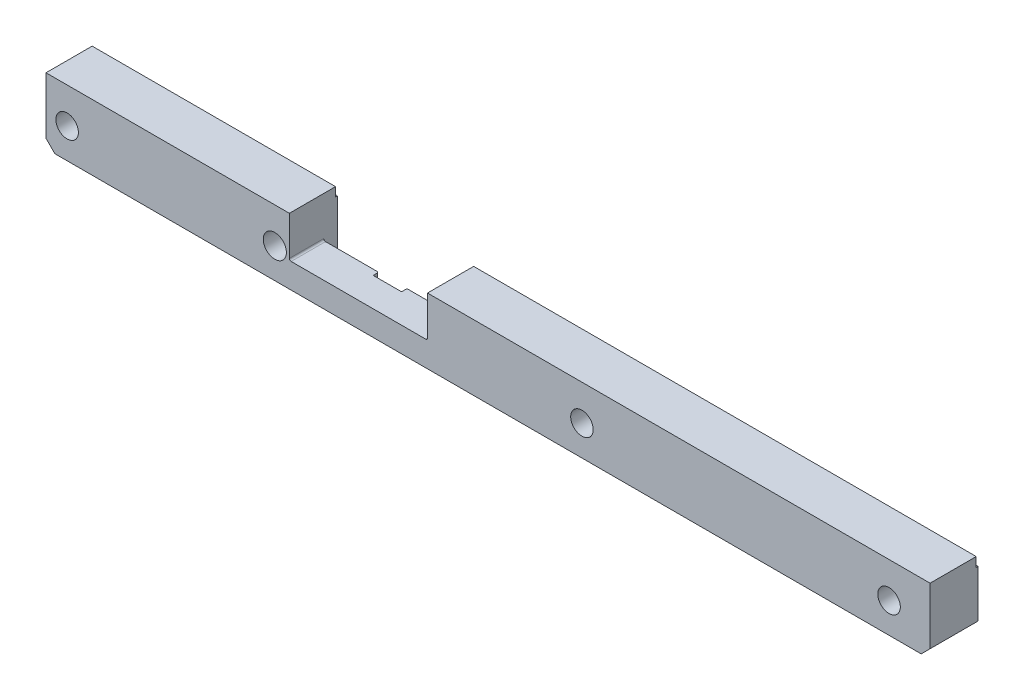
SolidWorks part; units mm, degrees
ref_plane "Front Plane" through (0, 0, 0) normal (0, 0, 1) x (1, 0, 0)
ref_plane "Top Plane" through (0, 0, 0) normal (0, 1, 0) x (1, 0, 0)
ref_plane "Right Plane" through (0, 0, 0) normal (1, 0, 0) x (0, 0, -1)
sketch "Sketch1" plane through (0, 0, 0) normal (0, 0, 1) x (1, 0, 0)
  line L1 (-151.0977, 41.5943) -> (346.9023, 41.5943)
  line L2 (-151.0977, 41.5943) -> (-151.0977, 4.5943)
  line L3 (-151.0977, 4.5943) -> (346.9023, 4.5943)
  line L4 (346.9023, 41.5943) -> (346.9023, 4.5943)
  dimension "D1" = 498
  dimension "D2" = 37
extrude "Boss-Extrude1" add sketch "Sketch1" along normal blind 27
sketch "Sketch3" plane through (0, 0, 0) normal (0, 0, -1) x (-1, 0, 0)
  line L0 (151.0977, 4.5943) -> (-346.9023, 4.5943) construction
  line L1 (-264.9023, 4.5943) -> (-294.9023, 4.5943)
  line L2 (-264.9023, 4.5943) -> (-264.9023, 31.5943)
  line L3 (-264.9023, 31.5943) -> (-294.9023, 31.5943)
  line L4 (-294.9023, 4.5943) -> (-294.9023, 31.5943)
  line L5 (-346.9023, 4.5943) -> (-346.9023, 41.5943) construction
  dimension "D1" = 27
  dimension "D2" = 52
  dimension "D3" = 82
extrude "Cut-Extrude2" cut sketch "Sketch3" against normal blind 4
sketch "Sketch4" plane through (0, 0, 0) normal (0, 0, -1) x (-1, 0, 0)
  line L0 (-346.9023, 41.5943) -> (151.0977, 41.5943) construction
  line L1 (13.9977, 41.5943) -> (-63.8023, 41.5943)
  line L2 (13.9977, 41.5943) -> (13.9977, 18.5943)
  line L3 (13.9977, 18.5943) -> (-63.8023, 18.5943)
  line L4 (-63.8023, 41.5943) -> (-63.8023, 18.5943)
  line L5 (-346.9023, 4.5943) -> (-346.9023, 41.5943) construction
  dimension "D1" = 283.1
  dimension "D2" = 360.9
  dimension "D3" = 23
extrude "Cut-Extrude3" cut sketch "Sketch4" against normal through all
sketch "Sketch5" plane through (0, 18.5943, 0) normal (0, 1, 0) x (1, 0, 0)
  line L0 (63.8023, -27) -> (63.8023, 0) construction
  line L1 (-13.9977, 0) -> (63.8023, 0)
  line L2 (-13.9977, 0) -> (-13.9977, -7.65)
  line L3 (-13.9977, -7.65) -> (63.8023, -7.65)
  line L4 (63.8023, 0) -> (63.8023, -7.65)
  line L5 (63.8023, -27) -> (-13.9977, -27) construction
  dimension "D1" = 19.35
extrude "Cut-Extrude4" cut sketch "Sketch5" against normal through all
sketch "Sketch6" plane through (0, 0, 7.65) normal (0, 0, -1) x (-1, 0, 0)
  line L0 (13.9977, 4.5943) -> (-63.8023, 4.5943) construction
  line L1 (-16.9023, 4.5943) -> (-32.9023, 4.5943)
  line L2 (-16.9023, 4.5943) -> (-16.9023, 18.5943)
  line L3 (-16.9023, 18.5943) -> (-32.9023, 18.5943)
  line L4 (-32.9023, 4.5943) -> (-32.9023, 18.5943)
  line L5 (13.9977, 18.5943) -> (-63.8023, 18.5943) construction
  line L6 (-346.9023, 4.5943) -> (-346.9023, 41.5943) construction
  point P10 (-16.9023, 11.5943)
  dimension "D1" = 314
  dimension "D2" = 330
extrude "Cut-Extrude5" cut sketch "Sketch6" against normal blind 3.05
sketch "Sketch7" plane through (0, 0, 0) normal (0, 0, -1) x (-1, 0, 0)
  line L0 (151.0977, 36.2546) -> (146.0977, 37.5943)
  line L1 (151.0977, 41.5943) -> (151.0977, 4.5943) construction
  line L2 (146.0977, 37.5943) -> (18.2423, 37.5943)
  line L3 (18.2423, 37.5943) -> (13.9977, 36.457)
  line L4 (13.9977, 4.5943) -> (13.9977, 41.5943) construction
  line L5 (13.9977, 36.457) -> (13.9977, 37.5943)
  line L6 (13.9977, 37.5943) -> (-63.8023, 37.5943)
  line L7 (-63.8023, 41.5943) -> (-63.8023, 4.5943) construction
  line L8 (-63.8023, 37.5943) -> (-341.9023, 37.5943)
  line L11 (-341.9023, 37.5943) -> (-346.9023, 36.2546)
  line L12 (-346.9023, 4.5943) -> (-346.9023, 41.5943) construction
  line L13 (-346.9023, 36.2546) -> (-346.9023, 41.5943)
  line L14 (-346.9023, 41.5943) -> (151.0977, 41.5943)
  line L15 (151.0977, 41.5943) -> (151.0977, 36.2546)
  dimension "D1" = 5
  dimension "D2" = 15
  dimension "D3" = 15
  dimension "D4" = 4
  dimension "D5" = 4
  dimension "D6" = 5
extrude "Cut-Extrude6" cut sketch "Sketch7" against normal blind 1
hole_wizard "M3 Tapped Hole1" positions "Sketch8" profile "Sketch9" tap size "M3" standard "ISO"
sketch "Sketch8" plane through (0, 4.5943, 0) normal (0, -1, 0) x (-1, 0, 0)
  line L0 (-346.9023, -27) -> (-346.9023, 0) construction
  line L1 (151.0977, -27) -> (-346.9023, -27) construction
  point P0 (-286.4023, -11.76)
  point P2 (-273.4023, -11.76)
  dimension "D1" = 60.5
  dimension "D2" = 73.5
  dimension "D3" = 15.24
sketch "Sketch9" plane through (286.4023, 4.5943, 11.76) normal (1, 0, 0) x (0, 0, -1)
  line L0 (0, 0) -> (0, 6.7511)
  line L1 (0, 6.7511) -> (1.25, 6)
  line L2 (1.25, 6) -> (1.25, 0)
  line L5 (1.25, 0) -> (0, 0)
  line L10 (0, 6.7511) -> (-1.25, 6) construction
  line L11 (0, -6.35) -> (0, 107.95) construction
  dimension "Tap Drill Dia." = 2.5
  dimension "Tap Drill Depth" = 6
  dimension "Drill Angle" = 118
cosmetic thread "Hole Thread1" parameters "D1"=6, "D2"=3
cosmetic thread "Hole Thread2" parameters "D1"=6, "D2"=3
hole_wizard "M4 Tapped Hole1" positions "Sketch10" profile "Sketch11" tap size "M4" standard "ISO"
sketch "Sketch10" plane through (0, 0, 7.65) normal (0, 0, -1) x (-1, 0, 0)
  line L0 (-346.9023, 4.5943) -> (-346.9023, 36.2546) construction
  line L1 (13.9977, 18.5943) -> (-16.9023, 18.5943) construction
  line L2 (-32.9023, 18.5943) -> (-63.8023, 18.5943) construction
  point P0 (5.0977, 11.5943)
  point P2 (-54.9023, 11.5943)
  dimension "D1" = 352
  dimension "D2" = 292
  dimension "D3" = 7
  dimension "D4" = 7
sketch "Sketch11" plane through (-5.0977, 11.5943, 7.65) normal (1, 0, 0) x (0, 1, 0)
  line L0 (0, 0) -> (0, 8.9914)
  line L1 (0, 8.9914) -> (1.65, 8)
  line L2 (1.65, 8) -> (1.65, 0)
  line L5 (1.65, 0) -> (0, 0)
  line L10 (0, 8.9914) -> (-1.65, 8) construction
  line L11 (0, -6.35) -> (0, 107.95) construction
  dimension "Tap Drill Dia." = 3.3
  dimension "Tap Drill Depth" = 8
  dimension "Drill Angle" = 118
cosmetic thread "Hole Thread3" parameters "D1"=8, "D2"=4
cosmetic thread "Hole Thread4" parameters "D1"=8, "D2"=4
hole_wizard "M3 Tapped Hole2" positions "Sketch12" profile "Sketch13" tap size "M3" standard "ISO"
sketch "Sketch12" plane through (0, 0, 0) normal (0, 0, -1) x (-1, 0, 0)
  line L0 (151.0977, 41.5943) -> (13.9977, 41.5943) construction
  line L1 (-346.9023, 4.5943) -> (-346.9023, 36.2546) construction
  point P0 (71.0977, 31.5943)
  point P2 (41.0977, 31.5943)
  point P4 (-99.9023, 31.5943)
  point P6 (-151.9023, 31.5943)
  point P8 (-206.9023, 31.5943)
  point P10 (-221.9023, 31.5943)
  point P12 (-354.5924, -112.4577)
  dimension "D1" = 10
  dimension "D2" = 418
  dimension "D3" = 388
  dimension "D4" = 247
  dimension "D5" = 195
  dimension "D6" = 140
  dimension "D7" = 125
sketch "Sketch13" plane through (-71.0977, 31.5943, 0) normal (1, 0, 0) x (0, 1, 0)
  line L0 (0, 0) -> (0, 6.7511)
  line L1 (0, 6.7511) -> (1.25, 6)
  line L2 (1.25, 6) -> (1.25, 0)
  line L5 (1.25, 0) -> (0, 0)
  line L10 (0, 6.7511) -> (-1.25, 6) construction
  line L11 (0, -6.35) -> (0, 107.95) construction
  dimension "Tap Drill Dia." = 2.5
  dimension "Tap Drill Depth" = 6
  dimension "Drill Angle" = 118
cosmetic thread "Hole Thread5" parameters "D1"=6, "D2"=3
cosmetic thread "Hole Thread6" parameters "D1"=6, "D2"=3
cosmetic thread "Hole Thread7" parameters "D1"=6, "D2"=3
cosmetic thread "Hole Thread8" parameters "D1"=6, "D2"=3
cosmetic thread "Hole Thread9" parameters "D1"=6, "D2"=3
cosmetic thread "Hole Thread10" parameters "D1"=6, "D2"=3
hole_wizard "M3 Tapped Hole3" positions "Sketch14" profile "Sketch15" tap size "M3" standard "ISO"
sketch "Sketch14" plane through (0, 4.5943, 0) normal (0, -1, 0) x (-1, 0, 0)
  line L0 (-346.9023, -27) -> (-346.9023, 0) construction
  line L1 (151.0977, -27) -> (-346.9023, -27) construction
  point P0 (12.3977, -14.1)
  point P2 (4.3977, -14.1)
  dimension "D1" = 359.3
  dimension "D2" = 351.3
  dimension "D3" = 12.9
  dimension "D4" = 12.9
sketch "Sketch15" plane through (-12.3977, 4.5943, 14.1) normal (1, 0, 0) x (0, 0, -1)
  line L0 (0, 0) -> (0, 6.7511)
  line L1 (0, 6.7511) -> (1.25, 6)
  line L2 (1.25, 6) -> (1.25, 0)
  line L5 (1.25, 0) -> (0, 0)
  line L10 (0, 6.7511) -> (-1.25, 6) construction
  line L11 (0, -6.35) -> (0, 107.95) construction
  dimension "Tap Drill Dia." = 2.5
  dimension "Tap Drill Depth" = 6
  dimension "Drill Angle" = 118
cosmetic thread "Hole Thread11" parameters "D1"=6, "D2"=3
cosmetic thread "Hole Thread12" parameters "D1"=6, "D2"=3
sketch "Sketch16" plane through (0, 0, 0) normal (0, 0, -1) x (-1, 0, 0)
  line L0 (-63.8023, 4.5943) -> (-264.9023, 4.5943) construction
  line L1 (-79.4023, 4.5943) -> (-89.4023, 4.5943)
  line L2 (-79.4023, 4.5943) -> (-79.4023, 37.5943)
  line L3 (-79.4023, 37.5943) -> (-89.4023, 37.5943)
  line L4 (-89.4023, 4.5943) -> (-89.4023, 37.5943)
  line L5 (-341.9023, 37.5943) -> (-63.8023, 37.5943) construction
  line L6 (-346.9023, 4.5943) -> (-346.9023, 36.2546) construction
  dimension "D1" = 267.5
  dimension "D2" = 10
extrude "Cut-Extrude7" cut sketch "Sketch16" against normal blind 0.4
fillet "Fillet1" radius 1 2 edges at (-13.9977, 18.5943, 17.325) (63.8023, 18.5943, 17.325)
chamfer "Chamfer1" distance 0.5 angle 45 2 edges at (32.9023, 11.5943, 7.65) (16.9023, 11.5943, 7.65)
fillet "Fillet2" radius 1 2 edges at (294.9023, 31.5943, 2) (264.9023, 31.5943, 2)
chamfer "Chamfer2" distance 5 angle 45 2 edges at (346.9023, 4.5943, 13.5) (-151.0977, 4.5943, 13.5)
sketch "Sketch17" plane through (0, 0, 0) normal (0, 0, -1) x (-1, 0, 0)
  line L0 (-63.8023, 41.5943) -> (-346.9023, 41.5943) construction
  line L1 (-346.9023, 9.5943) -> (-346.9023, 36.2546) construction
  circle A0 centre (-323.9023, 27.5943) radius 1.5
  circle A1 centre (-337.9023, 27.5943) radius 1.5
  dimension "D1" = 3
  dimension "D2" = 14
  dimension "D3" = 23
  dimension "D4" = 9
extrude "Cut-Extrude8" cut sketch "Sketch17" against normal blind 6
sketch "Sketch19" plane through (0, 0, 27) normal (0, 0, 1) x (1, 0, 0)
  line L2 (-13.9977, 41.5943) -> (-151.0977, 41.5943) construction
  line L3 (346.9023, 41.5943) -> (63.8023, 41.5943) construction
  circle A0 centre (-139.1977, 21.5943) radius 6.3472
  circle A1 centre (-22.1977, 21.5943) radius 6.5285
  circle A2 centre (150.8023, 21.5943) radius 6.3472
  circle A3 centre (323.8023, 21.5943) radius 6.3472
  dimension "D1" = 20
  dimension "D2" = 20
  dimension "D3" = 20
  dimension "D4" = 20
extrude "Cut-Extrude9" cut sketch "Sketch19" against normal through all
hole_wizard "M3.5 Tapped Hole1" positions "Sketch21" profile "Sketch22" tap size "M3.5" standard "ISO"
sketch "Sketch21" plane through (0, 4.5943, 0) normal (0, -1, 0) x (-1, 0, 0)
  point P0 (-131.4205, -2.1745)
  point P3 (-131.4205, -14.1745)
  point P6 (-81.4205, -2.1745)
sketch "Sketch22" plane through (131.4205, 4.5943, 2.1745) normal (1, 0, 0) x (0, 0, -1)
  line L0 (0, 0) -> (0, 5.8712)
  line L1 (0, 5.8712) -> (1.45, 5)
  line L2 (1.45, 5) -> (1.45, 0)
  line L5 (1.45, 0) -> (0, 0)
  line L10 (0, 5.8712) -> (-1.45, 5) construction
  line L11 (0, -6.35) -> (0, 107.95) construction
  dimension "Tap Drill Dia." = 2.9
  dimension "Tap Drill Depth" = 5
  dimension "Drill Angle" = 118
cosmetic thread "Hole Thread20" parameters "D1"=5, "D2"=3.5
cosmetic thread "Hole Thread21" parameters "D1"=5, "D2"=3.5
cosmetic thread "Hole Thread22" parameters "D1"=5, "D2"=3.5
hole_wizard "M4 Tapped Hole3" positions "Sketch28" profile "Sketch29" tap size "M4" standard "ISO"
sketch "Sketch28" plane through (0, 0, 0) normal (0, 0, -1) x (-1, 0, 0)
  point P0 (-246.6891, 8.5943)
  point P3 (-246.6891, 20.5943)
sketch "Sketch29" plane through (246.6891, 8.5943, 0) normal (1, 0, 0) x (0, 1, 0)
  line L0 (0, 0) -> (0, 7.9914)
  line L1 (0, 7.9914) -> (1.65, 7)
  line L2 (1.65, 7) -> (1.65, 0)
  line L5 (1.65, 0) -> (0, 0)
  line L10 (0, 7.9914) -> (-1.65, 7) construction
  line L11 (0, -6.35) -> (0, 107.95) construction
  dimension "Tap Drill Dia." = 3.3
  dimension "Tap Drill Depth" = 7
  dimension "Drill Angle" = 118
cosmetic thread "Hole Thread18" parameters "D1"=7, "D2"=4
cosmetic thread "Hole Thread23" parameters "D1"=7, "D2"=4
